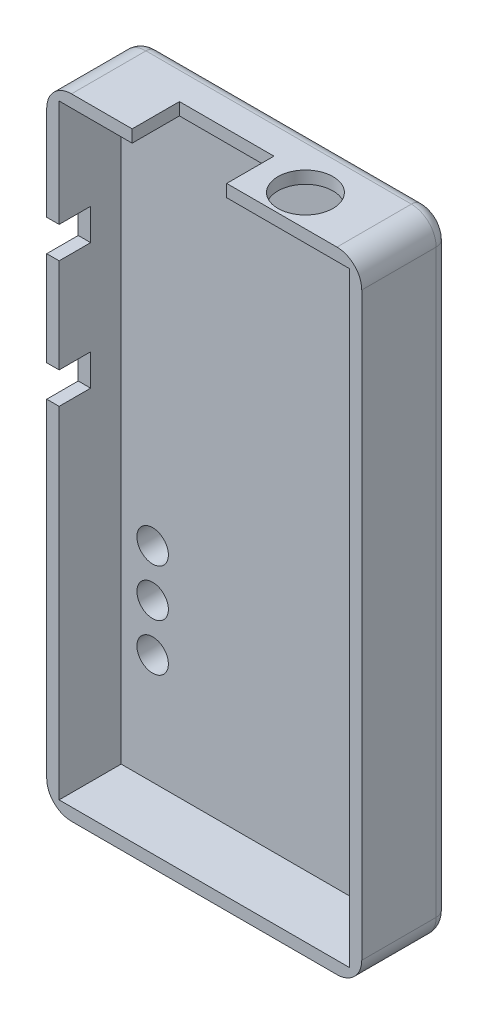
SolidWorks part; units mm, degrees
ref_plane "Front Plane" through (0, 0, 0) normal (0, 0, 1) x (1, 0, 0)
ref_plane "Top Plane" through (0, 0, 0) normal (0, 1, 0) x (1, 0, 0)
ref_plane "Right Plane" through (0, 0, 0) normal (1, 0, 0) x (0, 0, -1)
sketch "Sketch1" plane through (0, 0, 0) normal (0, 0, 1) x (1, 0, 0)
  line L1 (0, 0) -> (25.4, 0)
  line L2 (0, 0) -> (0, 50.8)
  line L3 (0, 50.8) -> (25.4, 50.8)
  line L4 (25.4, 0) -> (25.4, 50.8)
  dimension "D1" = 25.4
  dimension "D2" = 50.8
extrude "Boss-Extrude1" add sketch "Sketch1" along normal blind 2
sketch "Sketch2" plane through (0, 0, 2) normal (0, 0, 1) x (1, 0, 0)
  line L0 (25.4, 50.8) -> (0, 50.8) construction
  line L1 (24.4, 49.8) -> (1, 49.8)
  line L2 (24.4, 49.8) -> (24.4, 1)
  line L3 (24.4, 1) -> (1, 1)
  line L4 (1, 49.8) -> (1, 1)
  line L5 (25.4, 0) -> (25.4, 50.8) construction
  line L6 (0, -1.1) -> (0, 1.1) construction
  line L7 (1.1, 0) -> (-1.1, 0) construction
  line L8 (25.4, 50.8) -> (0, 50.8) construction
  line L9 (0, 50.8) -> (0, 0) construction
  line L10 (0, 0) -> (25.4, 0) construction
  line L11 (25.4, 0) -> (25.4, 50.8) construction
  line L12 (25.4, 50.8) -> (0, 50.8)
  line L13 (0, 50.8) -> (0, 0)
  line L14 (0, 0) -> (25.4, 0)
  line L15 (25.4, 0) -> (25.4, 50.8)
  dimension "D1" = 1
  dimension "D2" = 1
  dimension "D3" = 1
  dimension "D4" = 1
extrude "Boss-Extrude2" add sketch "Sketch2" along normal blind 5
fillet "Fillet1" radius 2 4 edges at (0, 0, 3.5) (25.4, 0, 3.5) (0, 50.8, 3.5) (25.4, 50.8, 3.5)
fillet "Fillet2" radius 1 8 edges at (24.8142, 0.5858, 0) (12.7, 0, 0) (0.5858, 0.5858, 0) (0, 25.4, 0) (0.5858, 50.2142, 0) (12.7, 50.8, 0) (24.8142, 50.2142, 0) (25.4, 25.4, 0)
sketch "Sketch6" plane through (0, 50.8, 0) normal (0, 1, 0) x (1, 0, 0)
  line L0 (23.4, -7) -> (23.4, -1) construction
  line L1 (23.4, -7) -> (2, -7) construction
  circle A0 centre (18.32, -4.46) radius 2.2225
  dimension "D2" = 4.445
  dimension "D1" = 5.08
  dimension "D3" = 2.54
extrude "Cut-Extrude3" cut sketch "Sketch6" against normal up to next
sketch "Sketch7" plane through (0, 50.8, 0) normal (0, 1, 0) x (1, 0, 0)
  line L0 (23.4, -7) -> (2, -7) construction
  line L1 (6.89, -7) -> (14.51, -7)
  line L2 (6.89, -7) -> (6.89, -3.19)
  line L3 (6.89, -3.19) -> (14.51, -3.19)
  line L4 (14.51, -7) -> (14.51, -3.19)
  line L5 (23.4, -7) -> (23.4, -1) construction
  dimension "D1" = 8.89
  dimension "D2" = 7.62
  dimension "D3" = 3.81
extrude "Cut-Extrude4" cut sketch "Sketch7" against normal up to next
sketch "Sketch8" plane through (0, 0, 0) normal (-1, 0, 0) x (0, 0, 1)
  line L0 (7, 48.8) -> (7, 2) construction
  line L1 (7, 41.18) -> (4.46, 41.18)
  line L2 (7, 41.18) -> (7, 38.64)
  line L3 (7, 38.64) -> (4.46, 38.64)
  line L4 (4.46, 41.18) -> (4.46, 38.64)
  line L5 (7, 48.8) -> (1, 48.8) construction
  line L7 (7, 31.02) -> (4.46, 31.02)
  line L8 (7, 31.02) -> (7, 28.48)
  line L9 (7, 28.48) -> (4.46, 28.48)
  line L10 (4.46, 31.02) -> (4.46, 28.48)
  dimension "D1" = 7.62
  dimension "D2" = 2.54
  dimension "D3" = 2.54
  dimension "D4" = 17.78
  dimension "D5" = 2.54
  dimension "D6" = 2.54
extrude "Cut-Extrude5" cut sketch "Sketch8" against normal up to next
sketch "Sketch9" plane through (0, 0, 0) normal (0, 0, -1) x (-1, 0, 0)
  line L0 (-23.4, 1) -> (-2, 1) construction
  line L1 (-1, 2) -> (-1, 48.8) construction
  circle A0 centre (-3.54, 9.89) radius 1.27
  circle A1 centre (-3.54, 13.7) radius 1.27
  circle A2 centre (-3.54, 17.51) radius 1.27
  dimension "D2" = 2.54
  dimension "D5" = 2.54
  dimension "D6" = 2.54
  dimension "D1" = 8.89
  dimension "D3" = 3.81
  dimension "D4" = 3.81
  dimension "D7" = 2.54
extrude "Cut-Extrude6" cut sketch "Sketch9" against normal up to next
equation "\"width\"=1"
equation "\"D1@Sketch1\"=\"width\""
equation "\"length\"=2"
equation "\"D2@Sketch1\"=\"length\""
equation "\"lip_thickness\"=0.0393701"
equation "\"D1@Sketch2\"=\"lip_thickness\""
equation "\"D2@Sketch2\"=\"lip_thickness\""
equation "\"D3@Sketch2\"=\"lip_thickness\""
equation "\"D4@Sketch2\"=\"lip_thickness\""
equation "\"container_thickness\"=0.0787402"
equation "\"D1@Boss-Extrude1\"=\"container_thickness\""
equation "\"lip_height\"= 5mm"
equation "\"D1@Boss-Extrude2\"=\"lip_height\""
equation "\"side_fillet\"= 2mm"
equation "\"D1@Fillet1\"=\"side_fillet\""
equation "\"face_fillet\"= 1mm"
equation "\"D1@Fillet2\"=\"face_fillet\""
equation "\"switch_offset\"=0.7"
equation "\"switch_length\"=0.1"
equation "\"switch_height\"=0.1"
equation "\"jack_offset\"=0.2"
equation "\"D1@Sketch6\" = \"jack_offset\""
equation "\"jack_diameter\"=0.175"
equation "\"D2@Sketch6\"=\"jack_diameter\""
equation "\"jack_offset2\"=0.1"
equation "\"D3@Sketch6\"=\"jack_offset2\""
equation "\"charger_offset\"=0.35"
equation "\"D1@Sketch7\"=\"charger_offset\""
equation "\"charget_width\"=0.3"
equation "\"D2@Sketch7\"=\"charget_width\""
equation "\"charger_height\"=0.15"
equation "\"D3@Sketch7\"=\"charger_height\""
equation "\"button_offset\"=0.3"
equation "\"D1@Sketch8\"=\"button_offset\""
equation "\"button_width\"=0.1"
equation "\"D2@Sketch8\"=\"button_width\""
equation "\"button_height\"=0.1"
equation "\"D3@Sketch8\"=\"button_height\""
equation "\"led_offset\"=0.35"
equation "\"D1@Sketch9\"=\"led_offset\""
equation "\"led_diameter\"=0.1"
equation "\"D2@Sketch9\"=\"led_diameter\""
equation "\"led_spacing\"=0.15"
equation "\"D3@Sketch9\"=\"led_spacing\""
equation "\"D4@Sketch9\"=\"led_spacing\""
equation "\"D5@Sketch9\"=\"led_diameter\""
equation "\"D6@Sketch9\"=\"led_diameter\""
equation "\"D4@Sketch8\"=\"switch_offset\""
equation "\"D5@Sketch8\"=\"switch_length\""
equation "\"D6@Sketch8\"=\"switch_height\""
